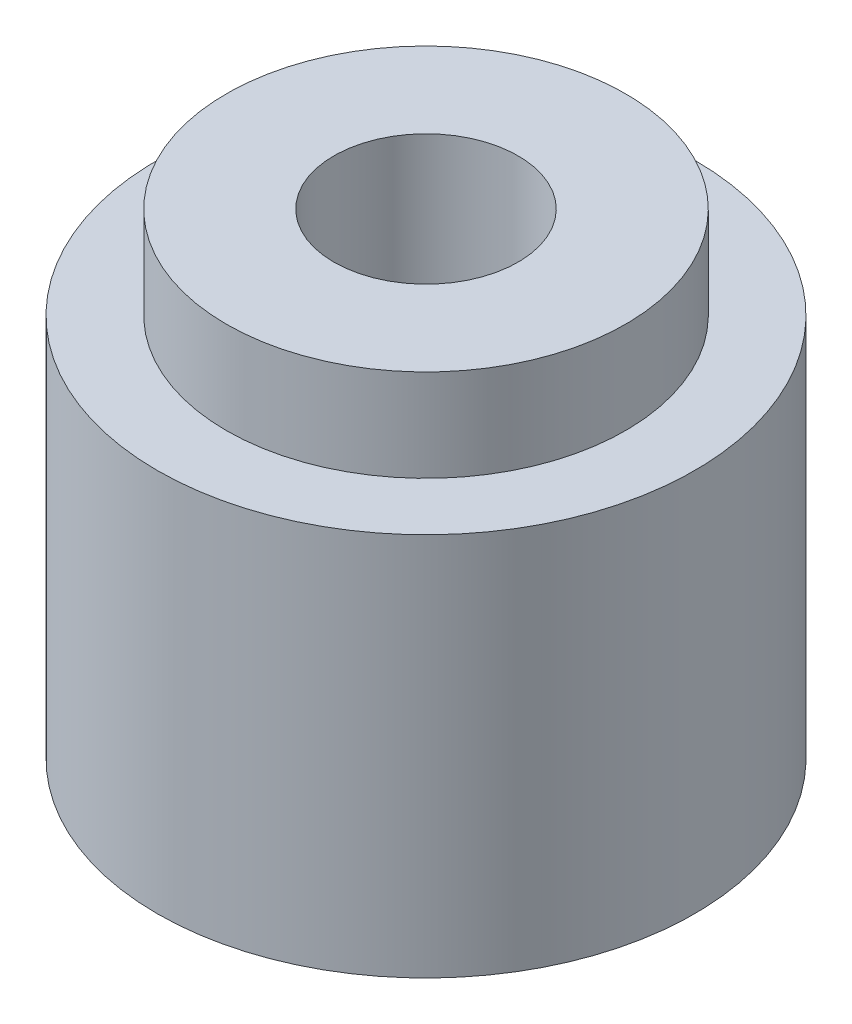
SolidWorks part; units mm, degrees
ref_plane "Front" through (0, 0, 0) normal (0, 0, 1) x (1, 0, 0)
ref_plane "Top" through (0, 0, 0) normal (0, 1, 0) x (1, 0, 0)
ref_plane "Right" through (0, 0, 0) normal (1, 0, 0) x (0, 0, -1)
sketch "Sketch1" plane through (0, 0, 0) normal (0, 1, 0) x (1, 0, 0)
  circle A0 centre (0, 0) radius 17.5
  dimension "D1" = 35
extrude "Boss-Extrude1" add sketch "Sketch1" along normal blind 25
sketch "Sketch2" plane through (0, 25, 0) normal (0, 1, 0) x (1, 0, 0)
  circle A0 centre (0, 0) radius 13
  dimension "D1" = 26
extrude "Boss-Extrude2" add sketch "Sketch2" along normal blind 6
sketch "Sketch3" plane through (0, 31, 0) normal (0, 1, 0) x (1, 0, 0)
  circle A0 centre (0, 0) radius 6
  dimension "D1" = 12
extrude "Cut-Extrude1" cut sketch "Sketch3" against normal through all
